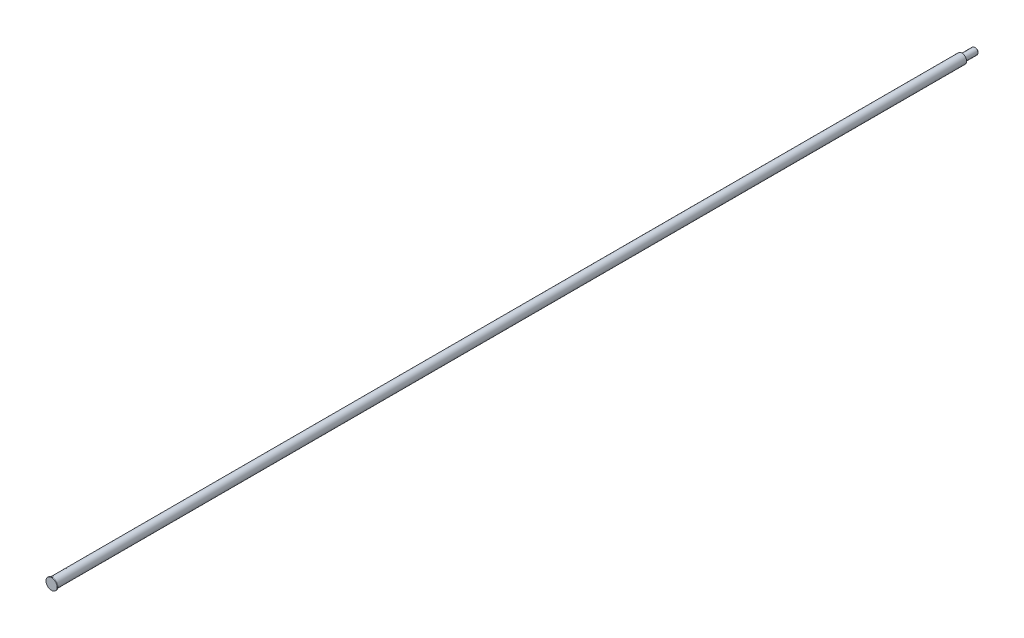
SolidWorks part; units mm, degrees
ref_plane "Plano frontal" through (0, 0, 0) normal (0, 0, 1) x (1, 0, 0)
ref_plane "Plano superior" through (0, 0, 0) normal (0, 1, 0) x (1, 0, 0)
ref_plane "Plano direito" through (0, 0, 0) normal (1, 0, 0) x (0, 0, -1)
ref_plane "Plano1" through (0, 0, 0) normal (0, -1, 0) x (1, 0, 0)
sketch "Esboço1" plane through (0, 0, 0) normal (0, -1, 0) x (1, 0, 0)
  line L0 (10.25, 0) -> (0, 0)
  line L1 (0, 0) -> (0, -1703.1002)
  line L2 (0, -1703.1002) -> (4.75, -1703.1002)
  line L3 (4.75, -1703.1002) -> (6, -1701.8502)
  line L4 (6, -1701.8502) -> (6, -1679.3502)
  line L5 (6, -1679.3502) -> (4.75, -1678.1002)
  line L6 (4.75, -1678.1002) -> (8.75, -1678.1002)
  line L7 (8.75, -1678.1002) -> (8.75, -1.6002)
  line L8 (8.75, -1.6002) -> (10.25, -1.6002)
  line L9 (10.25, -1.6002) -> (10.25, 0)
  line L10 (0, 0) -> (0, -1703.1002) construction
  dimension "D1" = 8.75
  dimension "D2" = 10.25
  dimension "D3" = 1.6002
  dimension "D4" = 1.25
  dimension "D5" = 45
  dimension "D6" = 1676.5
  dimension "D7" = 6
  dimension "D8" = 25
  dimension "D9" = 1.25
  dimension "D10" = 45
revolve "Revolução1" add sketch "Esboço1" angle 360 about L10
